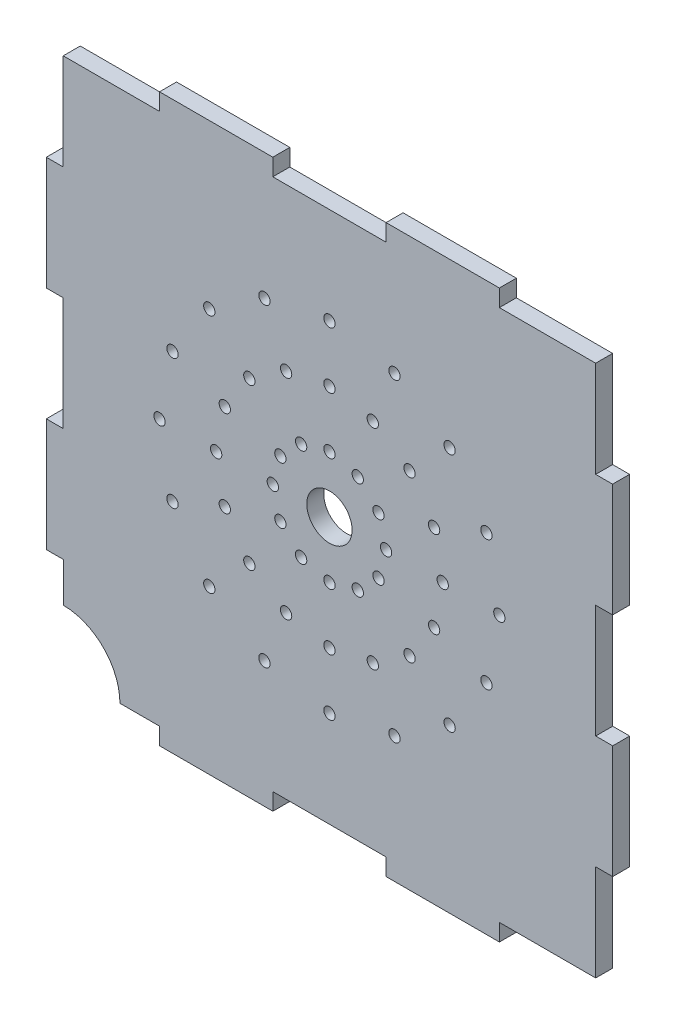
SolidWorks part; units mm, degrees
material "玻璃"
ref_plane "前视基准面" through (0, 0, 0) normal (0, 0, 1) x (1, 0, 0)
ref_plane "上视基准面" through (0, 0, 0) normal (0, 1, 0) x (1, 0, 0)
ref_plane "右视基准面" through (0, 0, 0) normal (1, 0, 0) x (0, 0, -1)
sketch "草图1" plane through (0, 0, 0) normal (0, 0, 1) x (1, 0, 0)
  line L0 (-39.9187, -39.9041) -> (47, 47.0244) construction
  line L21 (-10, 47.0244) -> (10, 47.0244)
  line L39 (10, 47.0244) -> (10, 50.0244)
  line L40 (10, 50.0244) -> (30, 50.0244)
  line L41 (30, 50.0244) -> (30, 47.0244)
  line L42 (30, 47.0244) -> (47, 47.0244)
  line L43 (-47, 47.0244) -> (47.0106, -46.9756) construction
  line L44 (47, 30.0244) -> (47, 47.0244)
  line L45 (49.9894, 30.0244) -> (47, 30.0244)
  line L46 (49.9894, 10.0244) -> (49.9894, 30.0244)
  line L47 (47.0106, 10.0244) -> (49.9894, 10.0244)
  line L48 (47.0106, -9.9756) -> (47.0106, 10.0244)
  line L50 (-47.0106, -9.9756) -> (-47.0106, 10.0244)
  line L51 (-47.0106, 10.0244) -> (-49.9894, 10.0244)
  line L52 (-49.9894, 10.0244) -> (-49.9894, 30.0244)
  line L53 (-49.9894, 30.0244) -> (-47, 30.0244)
  line L54 (-47, 30.0244) -> (-47, 47.0244)
  line L55 (-30, 47.0244) -> (-47, 47.0244)
  line L56 (-30, 50.0244) -> (-30, 47.0244)
  line L57 (-10, 50.0244) -> (-30, 50.0244)
  line L58 (-10, 47.0244) -> (-10, 50.0244)
  line L61 (-9.9894, -46.9756) -> (-9.9894, -49.9756)
  line L62 (-9.9894, -49.9756) -> (-29.9894, -49.9756)
  line L63 (-29.9894, -49.9756) -> (-29.9894, -46.9756)
  line L64 (-29.9894, -46.9756) -> (-36.9894, -46.9756)
  line L65 (-46.9894, -29.9756) -> (-46.9894, -36.9756)
  line L66 (-49.9894, -29.9756) -> (-46.9894, -29.9756)
  line L67 (-49.9894, -9.9756) -> (-49.9894, -29.9756)
  line L68 (-47.0106, -9.9756) -> (-49.9894, -9.9756)
  line L69 (47.0106, -9.9756) -> (50.0106, -9.9756)
  line L70 (50.0106, -9.9756) -> (50.0106, -29.9756)
  line L71 (50.0106, -29.9756) -> (47.0106, -29.9756)
  line L72 (47.0106, -29.9756) -> (47.0106, -46.9756)
  line L73 (30.0106, -46.9756) -> (47.0106, -46.9756)
  line L74 (30.0106, -49.9756) -> (30.0106, -46.9756)
  line L75 (10.0106, -49.9756) -> (30.0106, -49.9756)
  line L76 (10.0106, -46.9756) -> (10.0106, -49.9756)
  line L77 (-9.9894, -46.9756) -> (10.0106, -46.9756)
  circle A1 centre (10, 0) radius 1
  circle A2 centre (20, 0) radius 1
  circle A3 centre (30, 0) radius 1
  circle A5 centre (18.4777, -7.6533) radius 1
  circle A6 centre (27.7165, -11.4801) radius 1
  circle A8 centre (14.1424, -14.1414) radius 1
  circle A9 centre (21.2135, -21.2125) radius 1
  circle A11 centre (7.6543, -18.4767) radius 1
  circle A12 centre (11.4811, -27.7155) radius 1
  circle A14 centre (0.001, -19.999) radius 1
  circle A15 centre (0.001, -29.999) radius 1
  circle A17 centre (-7.6523, -18.4767) radius 1
  circle A18 centre (-11.4791, -27.7155) radius 1
  circle A20 centre (-14.1404, -14.1414) radius 1
  circle A21 centre (-21.2115, -21.2125) radius 1
  circle A23 centre (-18.4757, -7.6533) radius 1
  circle A24 centre (-27.7145, -11.4801) radius 1
  circle A26 centre (-19.998, 0) radius 1
  circle A27 centre (-29.998, 0) radius 1
  circle A29 centre (-18.4757, 7.6533) radius 1
  circle A30 centre (-27.7145, 11.4801) radius 1
  circle A32 centre (-14.1404, 14.1414) radius 1
  circle A33 centre (-21.2115, 21.2125) radius 1
  circle A35 centre (-7.6523, 18.4767) radius 1
  circle A36 centre (-11.4791, 27.7155) radius 1
  circle A38 centre (0.001, 19.999) radius 1
  circle A39 centre (0.001, 29.999) radius 1
  circle A41 centre (7.6543, 18.4767) radius 1
  circle A42 centre (11.4811, 27.7155) radius 1
  circle A44 centre (14.1424, 14.1414) radius 1
  circle A45 centre (21.2135, 21.2125) radius 1
  circle A47 centre (18.4777, 7.6533) radius 1
  circle A48 centre (27.7165, 11.4801) radius 1
  circle A49 centre (8.6603, -5) radius 1
  circle A50 centre (5, -8.6603) radius 1
  circle A51 centre (0, -10) radius 1
  circle A52 centre (-5, -8.6603) radius 1
  circle A53 centre (-8.6603, -5) radius 1
  circle A54 centre (-10, 0) radius 1
  circle A55 centre (-8.6603, 5) radius 1
  circle A56 centre (-5, 8.6603) radius 1
  circle A57 centre (0, 10) radius 1
  circle A58 centre (5, 8.6603) radius 1
  circle A59 centre (8.6603, 5) radius 1
  arc A60 (-36.9894, -46.9756) -> (-46.9894, -36.9756) centre (-46.9894, -46.9756) ccw
  circle A61 centre (0, 0) radius 4
  point P26 (0, 47.0244)
  point P36 (-47.0106, 0.0244)
  point P37 (47.0106, 0.0244)
  point P44 (0, -47)
  point P148 (0.001, 0)
  point P171 (0, 0)
  dimension "D1" = 20
  dimension "D2" = 10
  dimension "D3" = 17
  dimension "D4" = 3
  dimension "D5" = 3
  dimension "D7" = 16
  dimension "D8" = 12
extrude "凸台-拉伸1" add sketch "草图1" along normal blind 3
